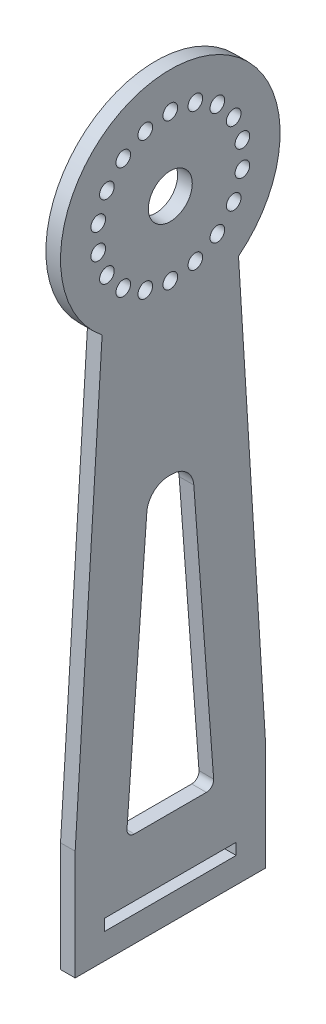
SolidWorks part; units mm, degrees
material "Fibra de Vidro S"
ref_plane "Plano frontal" through (0, 0, 0) normal (0, 0, 1) x (1, 0, 0)
ref_plane "Plano superior" through (0, 0, 0) normal (0, 1, 0) x (1, 0, 0)
ref_plane "Plano direito" through (0, 0, 0) normal (1, 0, 0) x (0, 0, -1)
sketch "Esboço1" plane through (0, 0, 0) normal (1, 0, 0) x (0, 0, -1)
  line L0 (-13, -71) -> (-13, -86)
  line L1 (-13, -86) -> (0, -86)
  line L3 (0, 15) -> (0, -86)
  arc A0 (0, 15) -> (-9.3165, -11.756) centre (0, 0) ccw
  spline S0 degree 1 poles (-9.3165, -11.756) (-13, -71) knots 0 0 1 1
  dimension "D1" = 30
  dimension "D4" = 15
  dimension "D5" = 86
extrude "Ressalto-extrusão1" add sketch "Esboço1" along normal blind 2
mirror "Espelhar1" about plane through (2, 15, 0) normal (0, 0, 1) of "Ressalto-extrusão1"
sketch "Esboço2" plane through (2, 0, 0) normal (1, 0, 0) x (0, 0, -1)
  circle A0 centre (0, 0) radius 3
  circle A1 centre (0, -10) radius 1
  dimension "D1" = 6
  dimension "D3" = 2
  dimension "D2" = 10
extrude "Corte-extrusão1" cut sketch "Esboço2" against normal blind 2
pattern_circular "PadrãoCircular1" count 18 every 20 about axis through (0, 0, 0) along (1, 0, 0) of "Corte-extrusão1"
sketch "Esboço3" plane through (2, 0, 0) normal (1, 0, 0) x (0, 0, -1)
  line L0 (-4.9222, -73) -> (4.9222, -73)
  line L1 (5.9194, -71.9252) -> (3.2082, -35.7756)
  line L2 (0.2166, -33) -> (-0.2166, -33)
  line L3 (-3.2082, -35.7756) -> (-5.9194, -71.9252)
  line L5 (-13, -86) -> (13, -86) construction
  line L6 (-9, -80.9386) -> (9, -80.9386)
  line L7 (-9, -80.9386) -> (-9, -82.5)
  line L8 (-9, -82.5) -> (9, -82.5)
  line L9 (9, -80.9386) -> (9, -82.5)
  line L10 (-9, -80.9386) -> (9, -82.5) construction
  line L11 (-9, -82.5) -> (9, -80.9386) construction
  arc A0 (0.2166, -33) -> (3.2082, -35.7756) centre (0.2166, -36) cw
  arc A1 (-0.2166, -33) -> (-3.2082, -35.7756) centre (-0.2166, -36) ccw
  arc A2 (4.9222, -73) -> (5.9194, -71.9252) centre (4.9222, -72) ccw
  arc A3 (-4.9222, -73) -> (-5.9194, -71.9252) centre (-4.9222, -72) cw
  point P6 (3, -33)
  point P9 (-3, -33)
  point P12 (6, -73)
  point P15 (-6, -73)
  point P16 (0, -81.7193)
  dimension "D4" = 3
  dimension "D5" = 1
  dimension "D1" = 12
  dimension "D2" = 6
  dimension "D3" = 40
  dimension "D6" = 18
  dimension "D7" = 3.5
extrude "Corte-extrusão2" cut sketch "Esboço3" against normal blind 2
